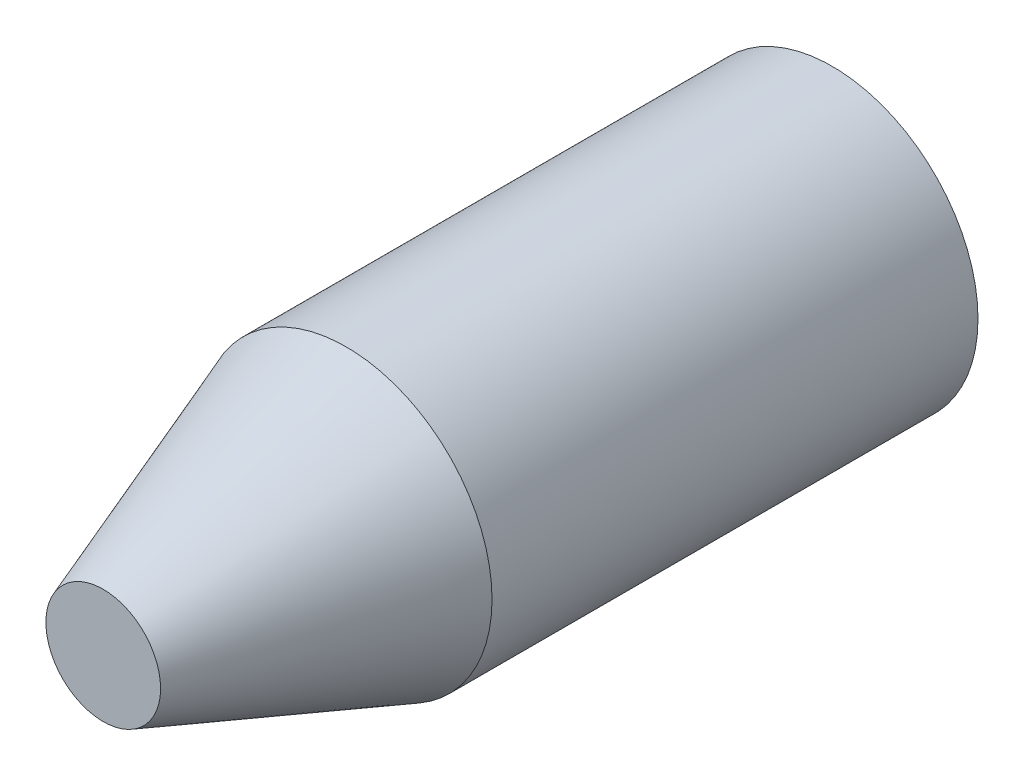
SolidWorks part; units mm, degrees
material "Brass"
ref_plane "Front Plane" through (0, 0, 0) normal (0, 0, 1) x (1, 0, 0)
ref_plane "Top Plane" through (0, 0, 0) normal (0, 1, 0) x (1, 0, 0)
ref_plane "Right Plane" through (0, 0, 0) normal (1, 0, 0) x (0, 0, -1)
sketch "Sketch1" plane through (0, 0, 0) normal (0, 0, 1) x (1, 0, 0)
  circle A0 centre (0, 0) radius 3
  dimension "D1" = 6
extrude "Boss-Extrude1" add sketch "Sketch1" along normal blind 10
sketch "Sketch2" plane through (0, 0, 10) normal (0, 0, 1) x (1, 0, 0)
  circle A0 centre (0, 0) radius 3
  circle A1 centre (0, 0) radius 3 construction
extrude "Boss-Extrude2" add sketch "Sketch2" along normal blind 5 draft 20
